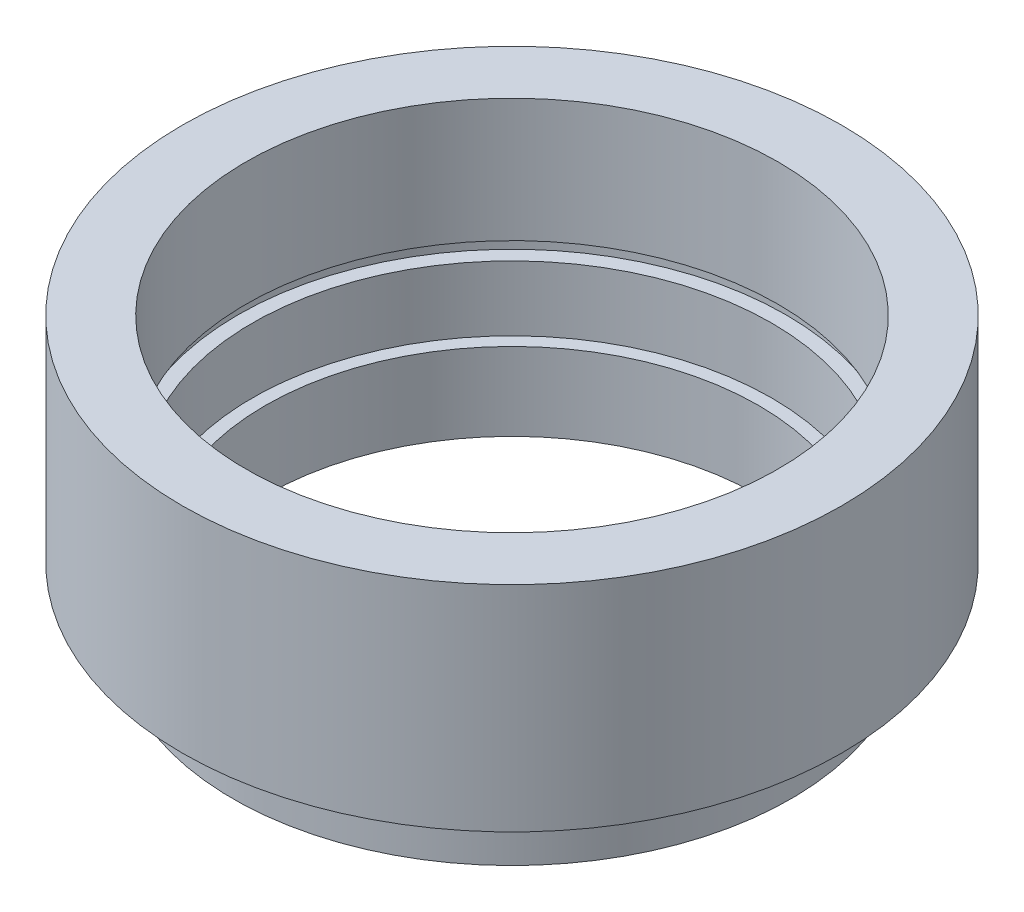
SolidWorks part; units mm, degrees
ref_plane "前视基准面" through (0, 0, 0) normal (0, 0, 1) x (1, 0, 0)
ref_plane "上视基准面" through (0, 0, 0) normal (0, 1, 0) x (1, 0, 0)
ref_plane "右视基准面" through (0, 0, 0) normal (1, 0, 0) x (0, 0, -1)
sketch "草图1" plane through (0, 0, 0) normal (0, 0, 1) x (1, 0, 0)
  line L0 (0, 0) -> (0, 21.8535) construction
  line L1 (19, 0) -> (21.5, 0)
  line L2 (21.5, 0) -> (21.5, 4)
  line L3 (21.5, 4) -> (20.5, 4)
  line L4 (20.5, 4) -> (20.5, 5)
  line L5 (20.5, 5) -> (25.4, 5)
  line L6 (25.4, 5) -> (25.4, 21.5)
  line L7 (25.4, 21.5) -> (20.5, 21.5)
  line L8 (20.5, 21.5) -> (20.5, 12)
  line L9 (20.5, 12) -> (21.1, 12)
  line L10 (21.1, 12) -> (21.1, 11)
  line L11 (21.1, 11) -> (20, 11)
  line L12 (20, 11) -> (20, 6)
  line L13 (20, 6) -> (19, 6)
  line L14 (19, 0) -> (19, 6)
  dimension "D1" = 21.5
  dimension "D2" = 25.4
  dimension "D3" = 20.5
  dimension "D4" = 20
  dimension "D5" = 1
  dimension "D6" = 5
  dimension "D7" = 19
  dimension "D8" = 21.5
  dimension "D9" = 1
  dimension "D10" = 5
  dimension "D11" = 6
  dimension "D12" = 21.1
  dimension "D13" = 20.5
revolve "旋转1" add sketch "草图1" angle 360 about L0
cosmetic thread "装饰螺纹线11" parameters "D2"=42
cosmetic thread "装饰螺纹线12" parameters "D2"=42
